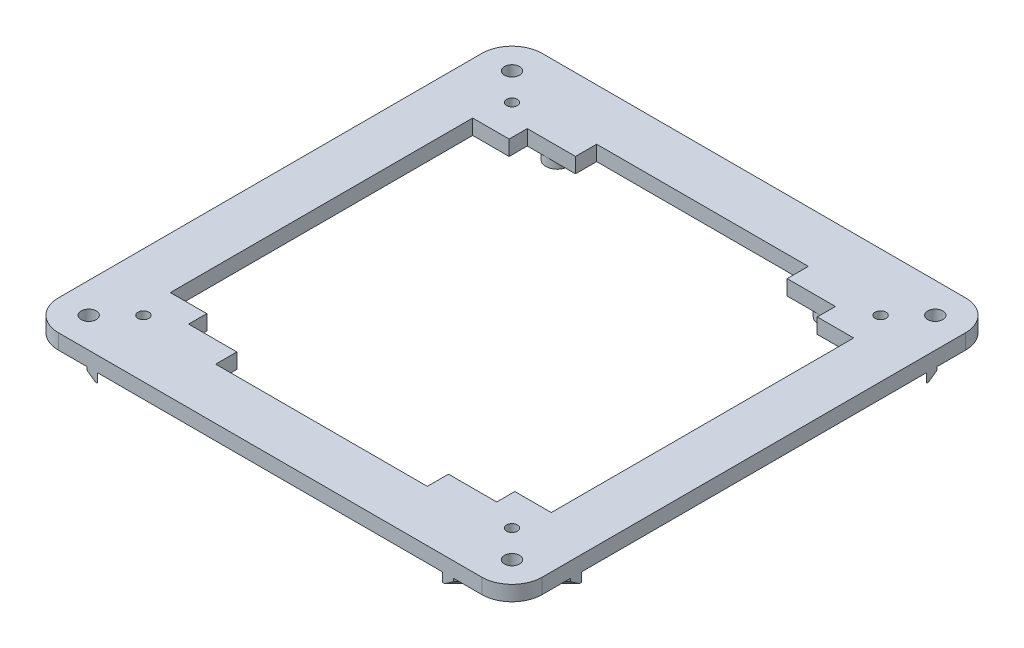
SolidWorks part; units mm, degrees
ref_plane "Front Plane" through (0, 0, 0) normal (0, 0, 1) x (1, 0, 0)
ref_plane "Top Plane" through (0, 0, 0) normal (0, 1, 0) x (1, 0, 0)
ref_plane "Right Plane" through (0, 0, 0) normal (1, 0, 0) x (0, 0, -1)
sketch "Sketch1" plane through (0, 0, 0) normal (0, 1, 0) x (1, 0, 0)
  line L0 (0, 0) -> (0, 25.4)
  line L1 (12.7, 38.1) -> (190.5, 38.1)
  line L2 (203.2, 25.4) -> (203.2, -152.4)
  line L3 (190.5, -165.1) -> (12.7, -165.1)
  line L4 (0, -152.4) -> (0, -127)
  line L5 (21.59, -127) -> (181.61, -127)
  line L6 (181.61, -127) -> (181.61, 0)
  line L7 (181.61, 0) -> (21.59, 0)
  line L10 (0, 0) -> (0, -127)
  line L12 (21.59, 0) -> (21.59, -127)
  arc A0 (12.7, -165.1) -> (0, -152.4) centre (12.7, -152.4) cw
  arc A1 (203.2, -152.4) -> (190.5, -165.1) centre (190.5, -152.4) cw
  arc A2 (190.5, 38.1) -> (203.2, 25.4) centre (190.5, 25.4) cw
  arc A3 (0, 25.4) -> (12.7, 38.1) centre (12.7, 25.4) cw
  point P13 (203.2, -165.1)
  point P16 (203.2, 38.1)
  point P19 (0, 38.1)
  dimension "D6" = 12.7
  dimension "D1" = 203.2
  dimension "D2" = 38.1
  dimension "D3" = 203.2
  dimension "D4" = 21.59
  dimension "D5" = 127
  dimension "D7" = 21.59
extrude "Boss-Extrude2" add sketch "Sketch1" along normal blind 6.35
sketch "Sketch2" plane through (0, 6.35, 0) normal (0, 1, 0) x (1, 0, 0)
  circle A0 centre (12.7, 25.4) radius 3.175
  circle A1 centre (190.5, 25.4) radius 3.175
  circle A2 centre (190.5, -152.4) radius 3.175
  circle A3 centre (12.7, -152.4) radius 3.175
  arc A4 (12.7, 38.1) -> (0, 25.4) centre (12.7, 25.4) ccw construction
  dimension "D1" = 6.35
extrude "Cut-Extrude1" cut sketch "Sketch2" against normal through all
sketch "Sketch8" plane through (0, 0, 0) normal (0, -1, 0) x (-1, 0, 0)
  line L0 (-3.7197, -161.3803) -> (-199.4803, 34.3803) construction
  line L1 (-24.1978, 13.9022) -> (-24.1978, 38.1) construction
  line L2 (-190.5, 38.1) -> (-12.7, 38.1) construction
  line L3 (-24.1978, 13.9022) -> (0, 13.9022) construction
  line L5 (-24.1978, 13.9022) -> (-3.7197, 34.3803) construction
  line L6 (0, 25.4) -> (0, -152.4) construction
  arc A0 (0, 25.4) -> (-12.7, 38.1) centre (-12.7, 25.4) ccw construction
  circle A1 centre (-24.1978, 13.9022) radius 2.286
  arc A2 (-12.7, -165.1) -> (0, -152.4) centre (-12.7, -152.4) ccw construction
  arc A3 (-190.5, 38.1) -> (-203.2, 25.4) centre (-190.5, 25.4) ccw construction
  circle A4 centre (-24.1978, -140.9022) radius 2.286
  circle A5 centre (-179.0022, -140.9022) radius 2.286
  circle A6 centre (-179.0022, 13.9022) radius 2.286
  point P8 (-101.6, -63.5)
  dimension "D2" = 4.572
  dimension "D1" = 28.9603
  dimension "D3" = 4
extrude "Cut-Extrude4" cut sketch "Sketch8" against normal through all
sketch "Sketch10" plane through (0, 0, 0) normal (0, -1, 0) x (-1, 0, 0)
  line L0 (-203.2, -152.4) -> (-203.2, 25.4) construction
  line L1 (-12.7, -165.1) -> (-190.5, -165.1) construction
  line L2 (-190.5, 38.1) -> (-12.7, 38.1) construction
  line L3 (0, 25.4) -> (0, -152.4) construction
  circle A0 centre (-44.45, -139.7) radius 2.286
  circle A1 centre (-158.75, -139.7) radius 2.286
  circle A2 centre (-158.75, 12.7) radius 2.286
  circle A3 centre (-44.45, 12.7) radius 2.286
  circle A4 centre (-44.45, 12.7) radius 4.826
  circle A5 centre (-158.75, 12.7) radius 4.826
  circle A6 centre (-158.75, -139.7) radius 4.826
  circle A7 centre (-44.45, -139.7) radius 4.826
  dimension "D1" = 4.572
  dimension "D2" = 44.45
  dimension "D3" = 25.4
  dimension "D4" = 25.4
  dimension "D5" = 44.45
  dimension "D6" = 2.54
extrude "Boss-Extrude3" add sketch "Sketch10" along normal blind 3.81
sketch "Sketch11" plane through (0, 0, 0) normal (0, -1, 0) x (1, 0, 0)
  line L0 (174.0713, -38.1) -> (187.3849, -24.7864)
  line L1 (190.5, -38.1) -> (12.7, -38.1) construction
  line L2 (203.2, 152.4) -> (203.2, -25.4) construction
  line L3 (203.2, -8.9713) -> (203.2, -13.4614)
  line L4 (203.2, -13.4614) -> (193.0933, -23.5682)
  line L5 (178.5614, -38.1) -> (174.0713, -38.1)
  line L6 (189.8864, -22.2849) -> (203.2, -8.9713)
  line L7 (188.6682, -27.9933) -> (178.5614, -38.1)
  line L8 (3.7197, -34.3803) -> (199.4803, 161.3803) construction
  line L9 (10.1067, -23.5682) -> (0, -13.4614)
  line L10 (0, -8.9713) -> (13.3136, -22.2849)
  line L11 (0, -13.4614) -> (0, -8.9713)
  line L12 (15.8151, -24.7864) -> (29.1287, -38.1)
  line L13 (24.6386, -38.1) -> (14.5318, -27.9933)
  line L14 (29.1287, -38.1) -> (24.6386, -38.1)
  line L15 (14.5318, 154.9933) -> (24.6386, 165.1)
  line L16 (29.1287, 165.1) -> (15.8151, 151.7864)
  line L17 (24.6386, 165.1) -> (29.1287, 165.1)
  line L18 (13.3136, 149.2849) -> (0, 135.9713)
  line L19 (0, 140.4614) -> (10.1067, 150.5682)
  line L20 (0, 135.9713) -> (0, 140.4614)
  line L21 (193.0933, 150.5682) -> (203.2, 140.4614)
  line L22 (203.2, 135.9713) -> (189.8864, 149.2849)
  line L23 (203.2, 140.4614) -> (203.2, 135.9713)
  line L24 (187.3849, 151.7864) -> (174.0713, 165.1)
  line L25 (178.5614, 165.1) -> (188.6682, 154.9933)
  line L26 (174.0713, 165.1) -> (178.5614, 165.1)
  arc A0 (187.3849, -24.7864) -> (188.6682, -27.9933) centre (190.5, -25.4) ccw
  arc A1 (193.0933, -23.5682) -> (189.8864, -22.2849) centre (190.5, -25.4) ccw
  arc A2 (0, -25.4) -> (12.7, -38.1) centre (12.7, -25.4) ccw construction
  arc A3 (203.2, 152.4) -> (190.5, 165.1) centre (190.5, 152.4) ccw construction
  arc A4 (13.3136, -22.2849) -> (10.1067, -23.5682) centre (12.7, -25.4) ccw
  arc A5 (14.5318, -27.9933) -> (15.8151, -24.7864) centre (12.7, -25.4) ccw
  arc A6 (15.8151, 151.7864) -> (14.5318, 154.9933) centre (12.7, 152.4) ccw
  arc A7 (10.1067, 150.5682) -> (13.3136, 149.2849) centre (12.7, 152.4) ccw
  arc A8 (189.8864, 149.2849) -> (193.0933, 150.5682) centre (190.5, 152.4) ccw
  arc A9 (188.6682, 154.9933) -> (187.3849, 151.7864) centre (190.5, 152.4) ccw
  point P22 (101.6, 63.5)
  dimension "D4" = 6.35
  dimension "D1" = 29.1287
  dimension "D2" = 29.1287
  dimension "D3" = 3.175
  dimension "D6" = 177.8
  dimension "D8" = 125.7236
  dimension "D5" = 4
extrude "Boss-Extrude4" add sketch "Sketch11" along normal blind 3.81
chamfer "Chamfer1" distance 2.54 angle 45 8 edges at (19.5852, -3.81, 160.0466) (5.0534, -3.81, 145.5148) (183.6148, -3.81, 160.0466) (198.1466, -3.81, 145.5148) (183.6148, -3.81, -33.0466) (198.1466, -3.81, -18.5148) (5.0534, -3.81, -18.5148) (19.5852, -3.81, -33.0466)
sketch "Sketch9" plane through (0, 6.35, 0) normal (0, 1, 0) x (1, 0, 0)
  line L0 (21.59, 0) -> (181.61, 0) construction
  line L1 (36.8978, 0) -> (166.3022, 0)
  line L2 (36.8978, 0) -> (36.8978, 7.62)
  line L3 (36.8978, 7.62) -> (57.15, 7.62)
  line L4 (166.3022, 0) -> (166.3022, 7.62)
  line L5 (181.61, -127) -> (21.59, -127) construction
  line L6 (166.3022, -127) -> (36.8978, -127)
  line L7 (166.3022, -127) -> (166.3022, -134.62)
  line L8 (166.3022, -134.62) -> (146.05, -134.62)
  line L9 (36.8978, -127) -> (36.8978, -134.62)
  line L11 (190.5, 38.1) -> (12.7, 38.1) construction
  line L14 (57.15, -134.62) -> (57.15, -143.51)
  line L15 (57.15, -143.51) -> (146.05, -143.51)
  line L16 (146.05, -134.62) -> (146.05, -143.51)
  line L18 (57.15, 7.62) -> (57.15, 16.51)
  line L19 (57.15, 16.51) -> (146.05, 16.51)
  line L20 (146.05, 7.62) -> (146.05, 16.51)
  line L21 (174.0713, 38.1) -> (29.1287, 38.1) construction
  line L22 (57.15, -134.62) -> (36.8978, -134.62)
  line L23 (146.05, 7.62) -> (166.3022, 7.62)
  circle A0 centre (179.0022, 13.9022) radius 2.286 construction
  circle A1 centre (24.1978, 13.9022) radius 2.286 construction
  circle A2 centre (44.45, 12.7) radius 2.286 construction
  point P30 (101.6, 16.51)
  point P31 (101.6, -127)
  point P32 (101.6, -143.51)
  dimension "D4" = 12.7
  dimension "D1" = 12.7
  dimension "D2" = 12.7
  dimension "D3" = 30.48
  dimension "D5" = 21.59
extrude "Cut-Extrude5" cut sketch "Sketch9" against normal through all
sketch "Sketch13" plane through (0, 0, 0) normal (0, -1, 0) x (1, 0, 0)
  line L0 (57.15, -7.62) -> (36.8978, -7.62) construction
  line L1 (54.61, -12.7) -> (74.295, -12.7)
  line L2 (54.61, -12.7) -> (54.61, -26.775)
  line L3 (54.61, -33.02) -> (74.295, -33.02)
  line L4 (148.59, -12.7) -> (148.59, -26.775)
  line L5 (174.0713, -38.1) -> (29.1287, -38.1) construction
  line L6 (99.06, -12.7) -> (79.375, -26.775)
  line L8 (99.06, -18.945) -> (99.06, -33.02)
  line L10 (104.14, -18.945) -> (104.14, -33.02)
  line L12 (123.825, -12.7) -> (123.825, -26.775)
  line L14 (128.905, -18.945) -> (128.905, -33.02)
  line L16 (74.295, -18.945) -> (74.295, -33.02)
  line L18 (79.375, -12.7) -> (79.375, -26.775)
  line L19 (128.905, -33.02) -> (148.59, -33.02)
  line L20 (79.375, -33.02) -> (99.06, -18.945)
  line L21 (128.905, -12.7) -> (148.59, -12.7)
  line L22 (104.14, -12.7) -> (123.825, -26.775)
  line L23 (104.14, -12.7) -> (123.825, -12.7)
  line L24 (104.14, -18.945) -> (123.825, -33.02)
  line L25 (128.905, -12.7) -> (148.59, -26.775)
  line L26 (-818.39, 63.5) -> (49181.61, 63.5) construction
  line L27 (148.59, -33.02) -> (128.905, -18.945)
  line L28 (104.14, -33.02) -> (123.825, -33.02)
  line L29 (74.295, -12.7) -> (54.61, -26.775)
  line L31 (54.61, -33.02) -> (74.295, -18.945)
  line L32 (79.375, -33.02) -> (99.06, -33.02)
  line L33 (79.375, -12.7) -> (99.06, -12.7)
  line L34 (181.61, 127) -> (181.61, 0) construction
  line L35 (79.375, 139.7) -> (99.06, 139.7)
  line L36 (79.375, 160.02) -> (99.06, 160.02)
  line L37 (54.61, 160.02) -> (74.295, 145.945)
  line L38 (74.295, 139.7) -> (54.61, 153.775)
  line L39 (104.14, 160.02) -> (123.825, 160.02)
  line L40 (148.59, 160.02) -> (128.905, 145.945)
  line L41 (128.905, 139.7) -> (148.59, 153.775)
  line L42 (104.14, 145.945) -> (123.825, 160.02)
  line L43 (104.14, 139.7) -> (123.825, 139.7)
  line L44 (104.14, 139.7) -> (123.825, 153.775)
  line L45 (128.905, 139.7) -> (148.59, 139.7)
  line L46 (79.375, 160.02) -> (99.06, 145.945)
  line L47 (128.905, 160.02) -> (148.59, 160.02)
  line L48 (79.375, 139.7) -> (79.375, 153.775)
  line L49 (74.295, 145.945) -> (74.295, 160.02)
  line L50 (128.905, 145.945) -> (128.905, 160.02)
  line L51 (123.825, 139.7) -> (123.825, 153.775)
  line L52 (104.14, 145.945) -> (104.14, 160.02)
  line L53 (99.06, 145.945) -> (99.06, 160.02)
  line L54 (99.06, 139.7) -> (79.375, 153.775)
  line L55 (148.59, 139.7) -> (148.59, 153.775)
  line L56 (54.61, 160.02) -> (74.295, 160.02)
  line L57 (54.61, 139.7) -> (54.61, 153.775)
  line L58 (54.61, 139.7) -> (74.295, 139.7)
  circle A0 centre (44.45, -12.7) radius 2.286 construction
  circle A1 centre (158.75, -12.7) radius 2.286 construction
  point P50 (181.61, 63.5)
  dimension "D1" = 5.08
  dimension "D2" = 5.08
  dimension "D3" = 10.16
  dimension "D4" = 10.16
  dimension "D5" = 5.08
  dimension "D6" = 5.08
  dimension "D7" = 5.08
  dimension "D8" = 5.08
  dimension "D9" = 5.08
  dimension "D10" = 5.08
  dimension "D11" = 5.08
  dimension "D12" = 93.98
